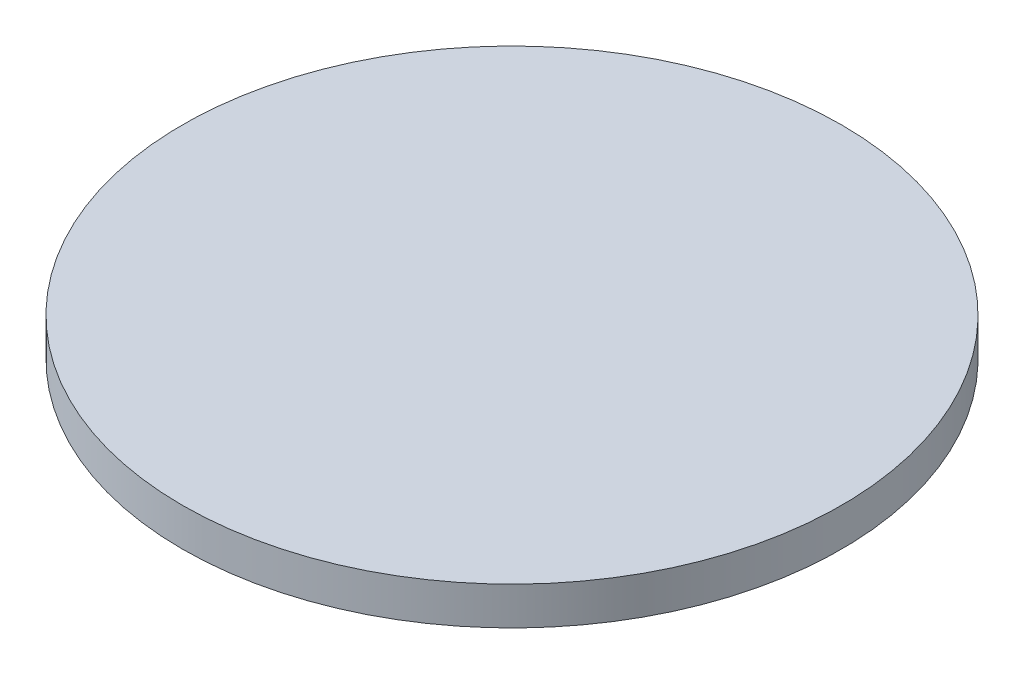
SolidWorks part; units mm, degrees
ref_plane "Front Plane" through (0, 0, 0) normal (0, 0, 1) x (1, 0, 0)
ref_plane "Top Plane" through (0, 0, 0) normal (0, 1, 0) x (1, 0, 0)
ref_plane "Right Plane" through (0, 0, 0) normal (1, 0, 0) x (0, 0, -1)
sketch "Sketch1" plane through (0, 0, 0) normal (0, 1, 0) x (1, 0, 0)
  circle A0 centre (0, 0) radius 83.82
  dimension "D1" = 167.64
extrude "Boss-Extrude1" add sketch "Sketch1" along normal mid plane 9.652
